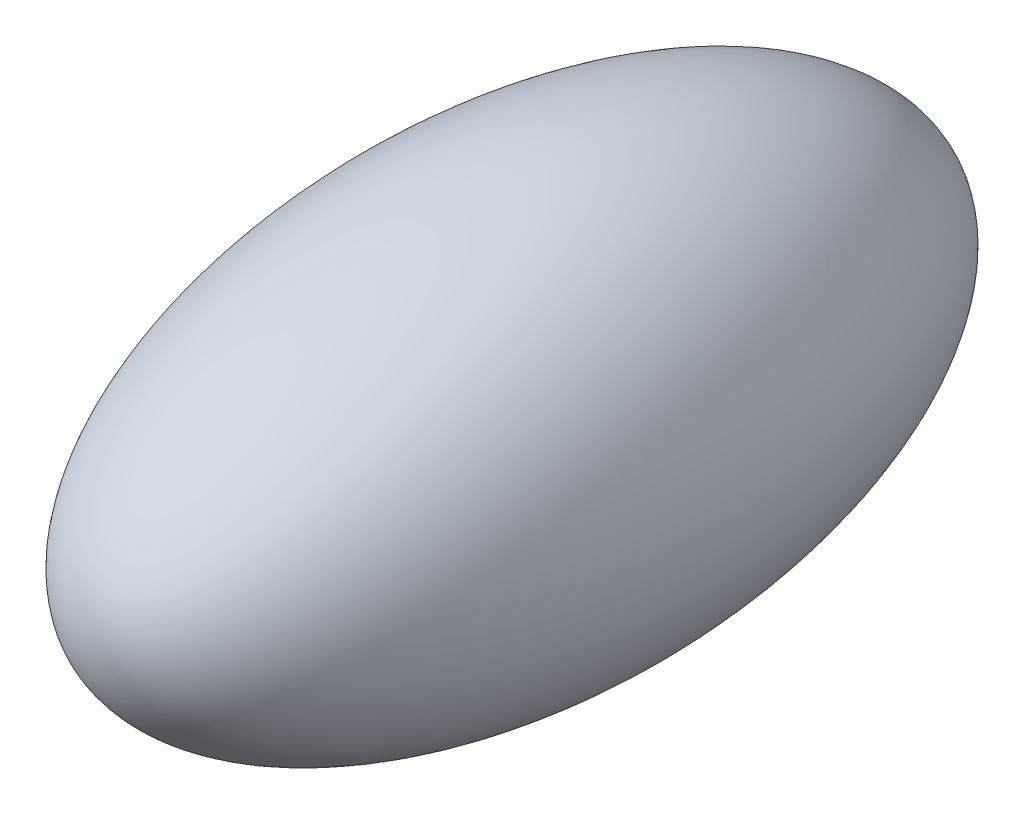
SolidWorks part; units mm, degrees
ref_plane "Front Plane" through (0, 0, 0) normal (0, 0, 1) x (1, 0, 0)
ref_plane "Top Plane" through (0, 0, 0) normal (0, 1, 0) x (1, 0, 0)
ref_plane "Right Plane" through (0, 0, 0) normal (1, 0, 0) x (0, 0, -1)
sketch "Sketch1" plane through (0, 0, 0) normal (1, 0, 0) x (0, 0, -1)
  line L0 (-12.7, 0) -> (12.7, 0) construction
  ellipse E0 centre (0, 0) end of major axis (12.7, 0) minor radius 6.35
  dimension "D1" = 25.4
  dimension "D2" = 12.7
revolve "Revolve2" add sketch "Sketch1" angle 360 about L0
